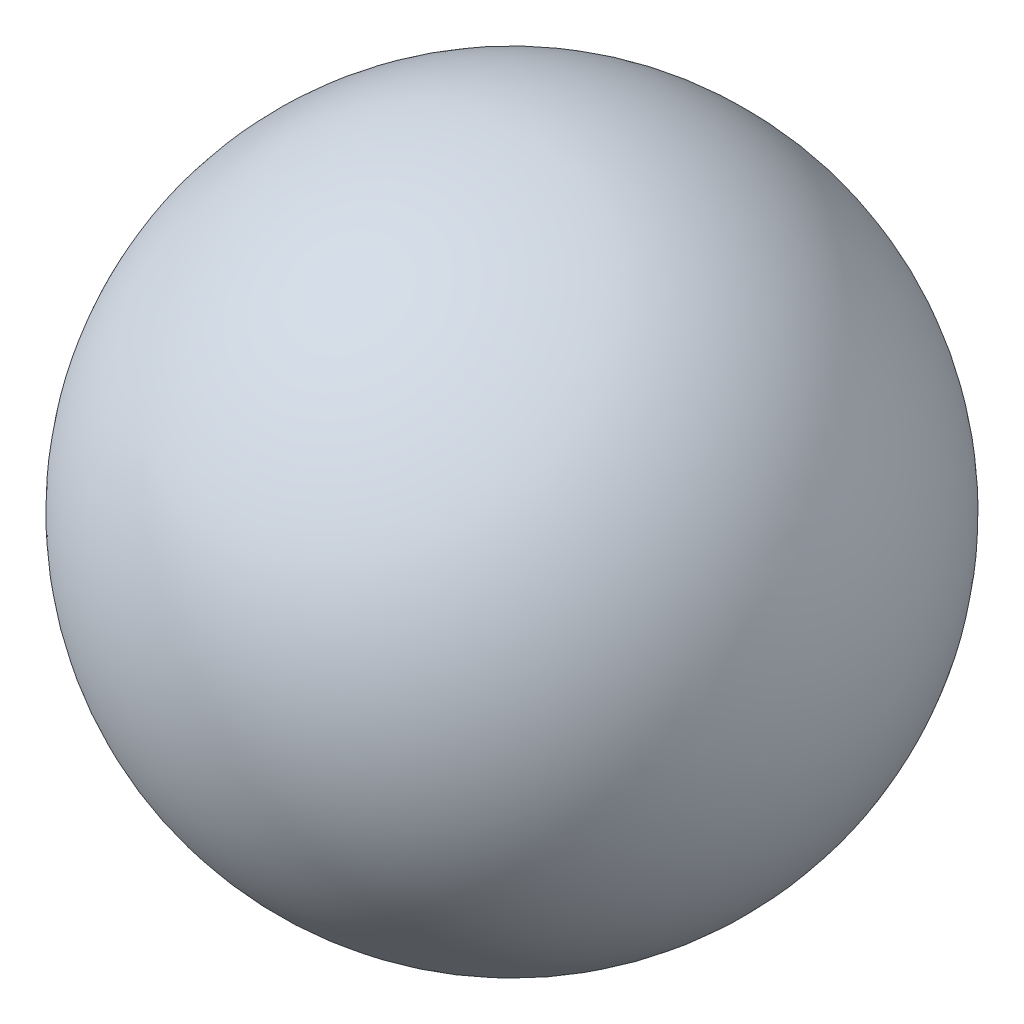
SolidWorks part; units mm, degrees
material "Silicon Rubber"
ref_plane "Front Plane" through (0, 0, 0) normal (0, 0, 1) x (1, 0, 0)
ref_plane "Top Plane" through (0, 0, 0) normal (0, 1, 0) x (1, 0, 0)
ref_plane "Right Plane" through (0, 0, 0) normal (1, 0, 0) x (0, 0, -1)
sketch "Sketch1" plane through (0, 0, 0) normal (0, 0, 1) x (1, 0, 0)
  line L0 (-76.2, 0) -> (76.2, 0)
  arc A0 (76.2, 0) -> (-76.2, 0) centre (0, 0) ccw
  dimension "D1" = 152.4
revolve "Revolve4" add sketch "Sketch1" angle 360 about L0
